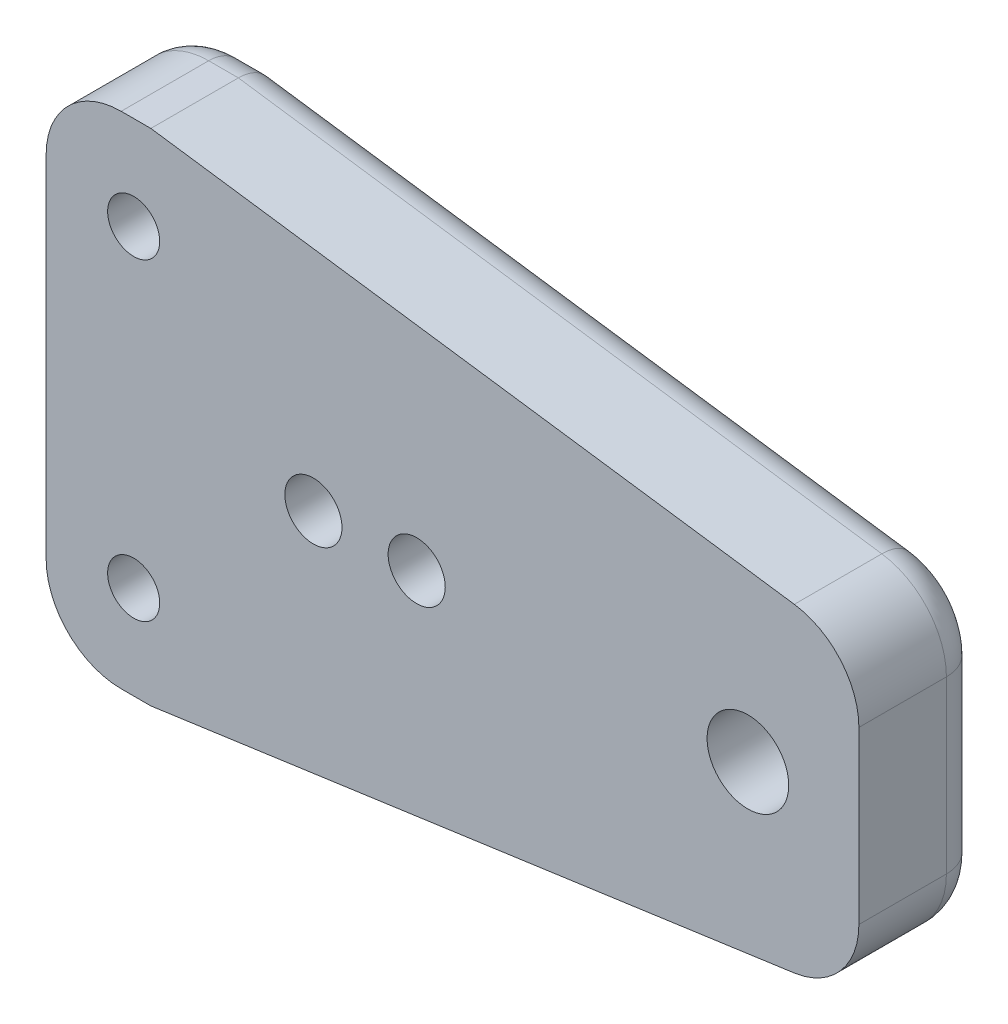
SolidWorks part; units mm, degrees
ref_plane "Front" through (0, 0, 0) normal (0, 0, 1) x (1, 0, 0)
ref_plane "Top" through (0, 0, 0) normal (0, 1, 0) x (1, 0, 0)
ref_plane "Right" through (0, 0, 0) normal (1, 0, 0) x (0, 0, -1)
sketch "Sketch1" plane through (0, 0, 0) normal (0, 0, 1) x (1, 0, 0)
  line L0 (-80, 0) -> (0, 0) construction
  line L1 (-90.1241, 20) -> (-87.7496, 20)
  line L2 (-96.1241, 14) -> (-96.1241, -14)
  line L3 (-90.1241, -20) -> (-87.7496, -20)
  line L4 (-31.1241, 6.8261) -> (-31.1241, -6.8261)
  line L5 (-36.2891, 12.7677) -> (-87.7496, 20)
  line L6 (0, 0) -> (-89.1241, -12.5256) construction
  line L7 (0, 0) -> (-89.1241, 12.5256) construction
  line L8 (-36.2891, -12.7677) -> (-87.7496, -20)
  circle A0 centre (0, 0) radius 90 construction
  circle A1 centre (-89.1241, 12.5256) radius 2.0828
  circle A2 centre (-40, 0) radius 3.2639
  circle A3 centre (-89.1241, -12.5256) radius 2.0828
  arc A4 (-90.1241, 20) -> (-96.1241, 14) centre (-90.1241, 14) ccw
  arc A5 (-90.1241, -20) -> (-96.1241, -14) centre (-90.1241, -14) cw
  arc A6 (-31.1241, -6.8261) -> (-36.2891, -12.7677) centre (-37.1241, -6.8261) cw
  arc A7 (-36.2891, 12.7677) -> (-31.1241, 6.8261) centre (-37.1241, 6.8261) cw
  point P17 (-96.1241, -20)
  point P22 (-31.1241, -12.0418)
  point P25 (-31.1241, 12.0418)
  dimension "D1" = 90
  dimension "D2" = 8
  dimension "D6" = 4.1656
  dimension "D9" = 6.5278
  dimension "D10" = 4.1656
  dimension "D12" = 6
  dimension "D4" = 6
  dimension "D3" = 40
  dimension "D5" = 65
  dimension "D7" = 58
  dimension "D8" = 8
  dimension "D11" = 40
extrude "Base-Extrude" add sketch "Sketch1" along normal blind 10
sketch "Sketch3" plane through (0, 0, 10) normal (0, 0, 1) x (1, 0, 0)
  line L0 (0, 0) -> (-105.2518, 0) construction
  line L1 (-31.1241, -6.8261) -> (-31.1241, 6.8261) construction
  circle A0 centre (-66.4896, 0) radius 2.285
  circle A1 centre (-74.7496, 0) radius 2.285
  dimension "D1" = 4.57
  dimension "D2" = 35.3655
  dimension "D3" = 8.26
extrude "Holes to Clamp" cut sketch "Sketch3" against normal through all
fillet "Fillet2" radius 3 10 edges at (-62.0194, -16.3838, 0) (-32.5959, -10.7624, 0) (-31.1241, 0, 0) (-32.5959, 10.7624, 0) (-88.9369, -20, 0) (-94.3668, -18.2426, 0) (-96.1241, 0, 0) (-62.0194, 16.3838, 0) (-88.9369, 20, 0) (-94.3668, 18.2426, 0)
